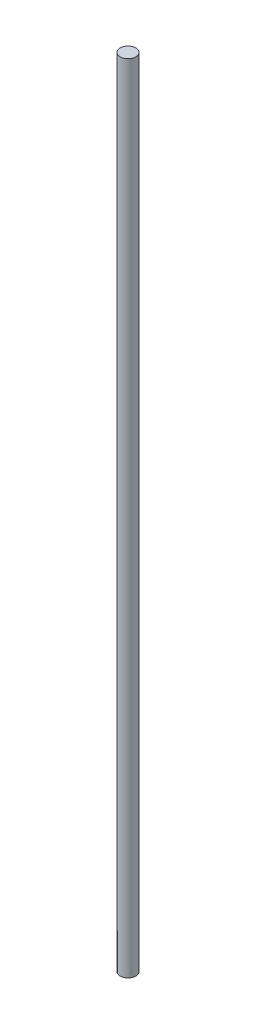
SolidWorks part; units mm, degrees
ref_plane "Front Plane" through (0, 0, 0) normal (0, 0, 1) x (1, 0, 0)
ref_plane "Top Plane" through (0, 0, 0) normal (0, 1, 0) x (1, 0, 0)
ref_plane "Right Plane" through (0, 0, 0) normal (1, 0, 0) x (0, 0, -1)
sketch "Sketch1" plane through (0, 0, 0) normal (0, 0, 1) x (1, 0, 0)
  line L0 (4, 204) -> (0, 204)
  line L1 (0, 204) -> (0, -204)
  line L2 (0, -204) -> (4, -204)
  line L3 (4, -204) -> (4, 204)
  line L4 (0, 204) -> (0, -204) construction
  dimension "D1" = 4
  dimension "xaxis" = 408
revolve "Revolve1" add sketch "Sketch1" angle 360 about L4
